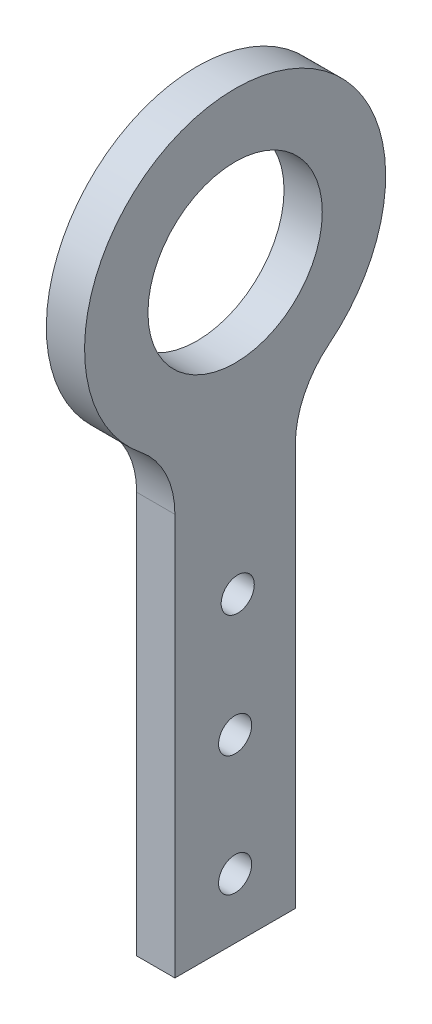
SolidWorks part; units mm, degrees
ref_plane "Front Plane" through (0, 0, 0) normal (0, 0, 1) x (1, 0, 0)
ref_plane "Top Plane" through (0, 0, 0) normal (0, 1, 0) x (1, 0, 0)
ref_plane "Right Plane" through (0, 0, 0) normal (1, 0, 0) x (0, 0, -1)
sketch "Sketch1" plane through (0, 0, 0) normal (1, 0, 0) x (0, 0, -1)
  line L0 (-10, -22.9129) -> (-10, -97.9129)
  line L1 (-10, -97.9129) -> (10, -97.9129)
  line L2 (10, -97.9129) -> (10, -22.9129)
  line L3 (-10, -22.9129) -> (10, -22.9129) construction
  circle A0 centre (0, 0) radius 14.475
  arc A2 (10, -22.9129) -> (-10, -22.9129) centre (0, 0) ccw
  point P8 (0, -22.9129)
  dimension "D3" = 28.95
  dimension "D4" = 50
  dimension "D1" = 20
  dimension "D2" = 97.9129
extrude "Boss-Extrude1" add sketch "Sketch1" along normal blind 6.35
sketch "Sketch2" plane through (6.35, 0, 0) normal (1, 0, 0) x (0, 0, -1)
  line L1 (-10, -97.9129) -> (10, -97.9129) construction
  circle A1 centre (0, -87.9129) radius 2.75
  circle A2 centre (0, -67.9129) radius 2.75
  circle A3 centre (0.4312, -47.9129) radius 2.75
  dimension "D1" = 20
  dimension "D2" = 5.5
  dimension "D3" = 5.5
  dimension "D4" = 10
  dimension "D8" = 5.5
  dimension "D6" = 20
extrude "Cut-Extrude1" cut sketch "Sketch2" against normal through all
fillet "Fillet1" radius 15 2 edges at (3.175, -22.9129, -10) (3.175, -22.9129, 10)
